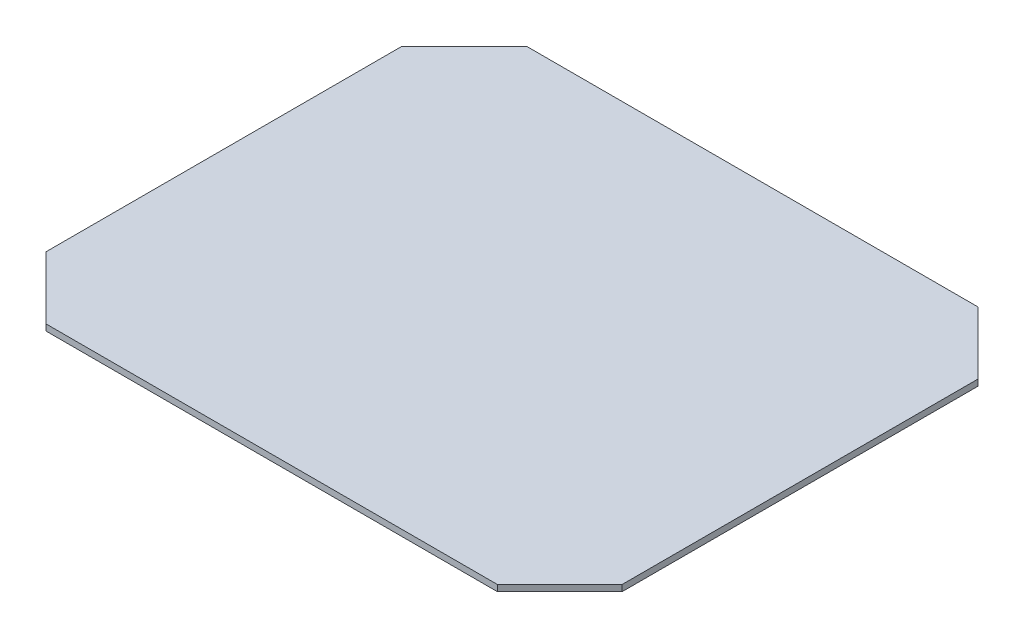
SolidWorks part; units mm, degrees
ref_plane "Front Plane" through (0, 0, 0) normal (0, 0, 1) x (1, 0, 0)
ref_plane "Top Plane" through (0, 0, 0) normal (0, 1, 0) x (1, 0, 0)
ref_plane "Right Plane" through (0, 0, 0) normal (1, 0, 0) x (0, 0, -1)
sketch "Sketch1" plane through (0, 0, 0) normal (0, 1, 0) x (1, 0, 0)
  line L0 (-459.105, 488.95) -> (-586.105, 361.95)
  line L1 (459.105, 488.95) -> (-459.105, 488.95)
  line L2 (586.105, 361.95) -> (586.105, -361.95)
  line L3 (459.105, -488.95) -> (-459.105, -488.95)
  line L4 (-586.105, 361.95) -> (-586.105, -361.95)
  line L5 (586.105, 488.95) -> (-586.105, -488.95) construction
  line L6 (586.105, -488.95) -> (-586.105, 488.95) construction
  line L7 (-459.105, -488.95) -> (-586.105, -361.95)
  line L8 (586.105, -361.95) -> (459.105, -488.95)
  line L9 (586.105, 361.95) -> (459.105, 488.95)
  point P0 (0, 0)
  dimension "D1" = 977.9
  dimension "D2" = 1172.21
extrude "Boss-Extrude1" add sketch "Sketch1" along normal mid plane 12.7
